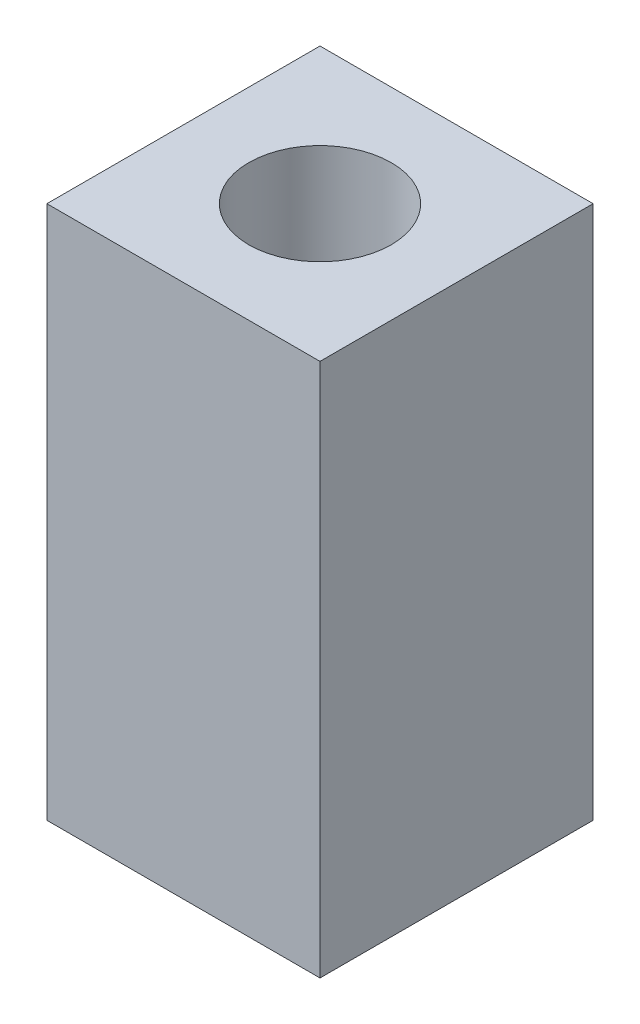
SolidWorks part; units mm, degrees
material "Thornel Mat VMA"
ref_plane "Front Plane" through (0, 0, 0) normal (0, 0, 1) x (1, 0, 0)
ref_plane "Top Plane" through (0, 0, 0) normal (0, 1, 0) x (1, 0, 0)
ref_plane "Right Plane" through (0, 0, 0) normal (1, 0, 0) x (0, 0, -1)
sketch "Sketch1" plane through (0, 0, 0) normal (0, 1, 0) x (1, 0, 0)
  line L1 (-5.7535, -5.7535) -> (5.7535, -5.7535)
  line L2 (-5.7535, -5.7535) -> (-5.7535, 5.7535)
  line L3 (-5.7535, 5.7535) -> (5.7535, 5.7535)
  line L4 (5.7535, -5.7535) -> (5.7535, 5.7535)
  line L5 (-5.7535, -5.7535) -> (5.7535, 5.7535) construction
  line L6 (-5.7535, 5.7535) -> (5.7535, -5.7535) construction
  circle A0 centre (0, 0) radius 3
  dimension "D1" = 6
  dimension "D2" = 11.5069
extrude "Boss-Extrude1" add sketch "Sketch1" along normal blind 22.5
